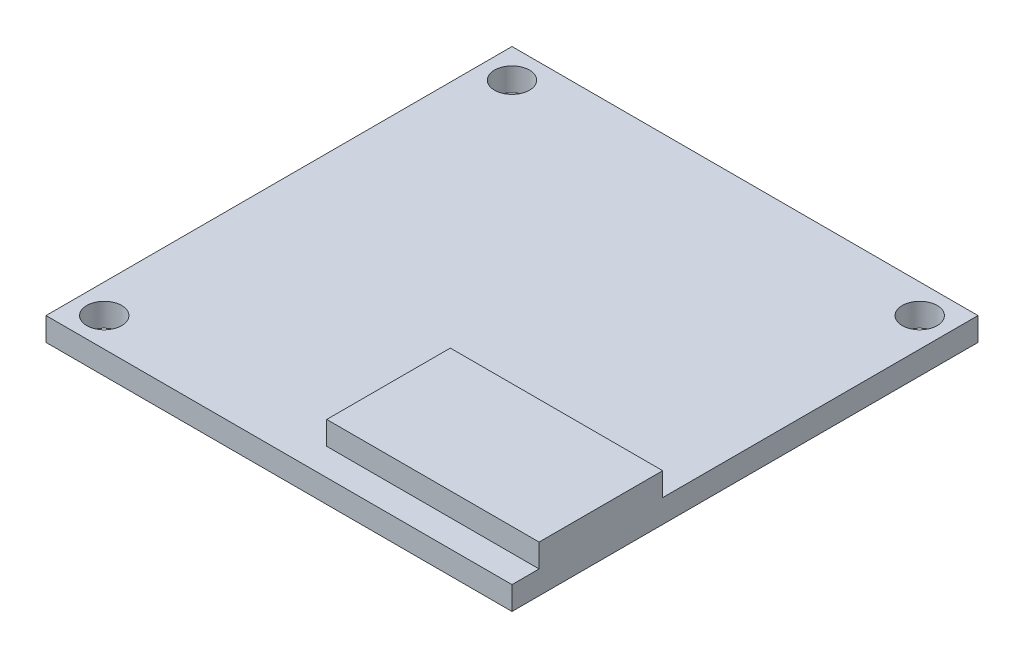
SolidWorks part; units mm, degrees
ref_plane "Front Plane" through (0, 0, 0) normal (0, 0, 1) x (1, 0, 0)
ref_plane "Top Plane" through (0, 0, 0) normal (0, 1, 0) x (1, 0, 0)
ref_plane "Right Plane" through (0, 0, 0) normal (1, 0, 0) x (0, 0, -1)
sketch "Sketch1" plane through (0, 0, 0) normal (0, 1, 0) x (1, 0, 0)
  line L1 (0, 0) -> (40, 0)
  line L2 (0, 0) -> (0, 40)
  line L3 (0, 40) -> (40, 40)
  line L4 (40, 0) -> (40, 40)
  dimension "D1" = 40
  dimension "D2" = 40
extrude "Boss-Extrude1" add sketch "Sketch1" along normal blind 2
sketch "Sketch2" plane through (0, 2, 0) normal (0, 1, 0) x (1, 0, 0)
  line L0 (20, 40) -> (20, 0) construction
  line L1 (40, 40) -> (0, 40) construction
  line L2 (0, 0) -> (40, 0) construction
  line L3 (0, 20) -> (40, 20) construction
  line L4 (0, 40) -> (0, 0) construction
  line L6 (40, 0) -> (40, 40) construction
  circle A0 centre (2.5, 37.5) radius 1.5
  circle A1 centre (37.5, 37.5) radius 1.5
  circle A2 centre (2.5, 2.5) radius 1.5
  dimension "D1" = 3
  dimension "D2" = 2.5
  dimension "D3" = 2.5
extrude "Cut-Extrude1" cut sketch "Sketch2" against normal through all
sketch "Sketch3" plane through (0, 2, 0) normal (0, 1, 0) x (1, 0, 0)
  line L0 (40, 0) -> (40, 40) construction
  line L1 (21.7702, 12.9356) -> (40, 12.9356)
  line L2 (21.7702, 12.9356) -> (21.7702, 2.3252)
  line L3 (21.7702, 2.3252) -> (40, 2.3252)
  line L4 (40, 12.9356) -> (40, 2.3252)
extrude "Boss-Extrude2" add sketch "Sketch3" along normal blind 2
